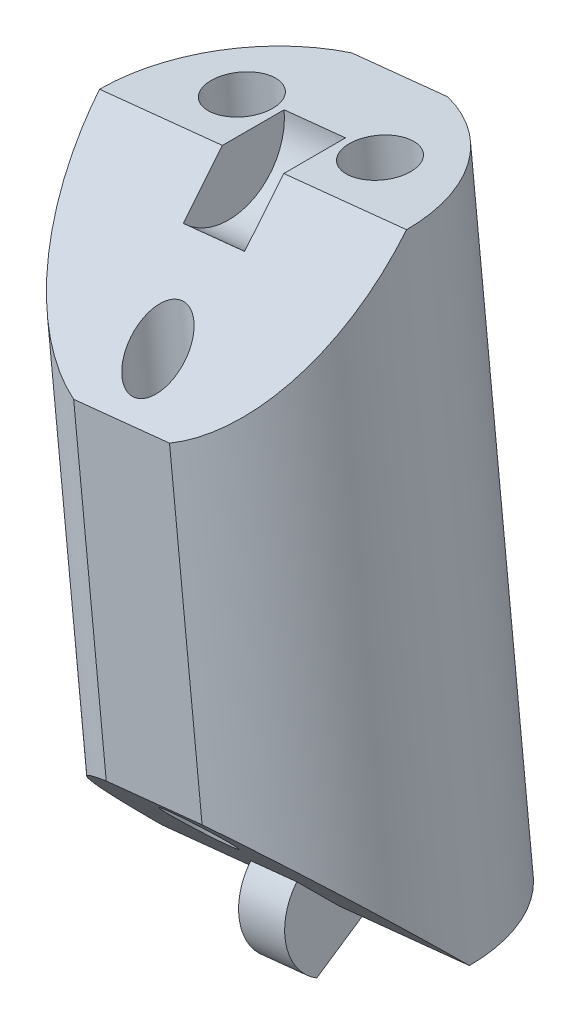
SolidWorks part; units mm, degrees
ref_plane "Front Plane" through (0, 0, 0) normal (0, 0, 1) x (1, 0, 0)
ref_plane "Top Plane" through (0, 0, 0) normal (0, 1, 0) x (1, 0, 0)
ref_plane "Right Plane" through (0, 0, 0) normal (1, 0, 0) x (0, 0, -1)
sketch "Sketch2" plane through (0, 0, 0) normal (0, 0, 1) x (1, 0, 0)
  line L0 (0, 0) -> (90, 0)
  line L1 (90, 0) -> (90, 120)
  line L2 (90, 120) -> (0, 120)
  line L3 (0, 120) -> (0, 0)
  line L4 (0, 120) -> (-10, 120)
  line L5 (-10, 120) -> (-10, 16.9491)
  line L6 (-10, 120) -> (57.5, 127)
  line L7 (57.5, 127) -> (90, 124)
  line L8 (90, 120) -> (99, 60)
  line L10 (90, 124) -> (90, 120)
  line L11 (5.9147, 0) -> (5.9147, -25)
  line L12 (5.9147, -25) -> (-4.0853, -25)
  line L13 (-4.0853, -29) -> (-4.0853, 0)
  line L14 (80, 0) -> (80, -25)
  line L15 (80, -25) -> (90, -25)
  line L16 (90, -29) -> (90, 0)
  line L17 (15.7927, 122.6748) -> (5.4776, 222.1414)
  line L18 (5.4776, 222.1414) -> (21.3923, 223.7918)
  line L19 (21.3923, 223.7918) -> (31.7073, 124.3252)
  line L20 (7.6492, 201.201) -> (23.5639, 202.8514)
  line L21 (10.9066, 169.7905) -> (26.8212, 171.441)
  line L22 (-10, 120) -> (-20.0396, 216.8108)
  line L23 (-20.0396, 216.8108) -> (-4.125, 218.4612)
  line L24 (-4.125, 218.4612) -> (5.9147, 121.6504)
  line L25 (-17.926, 196.4296) -> (-2.0114, 198.08)
  line L26 (-14.7556, 165.8578) -> (1.159, 167.5082)
  line L27 (57.5, 127) -> (46.9095, 229.1223)
  line L28 (46.9095, 229.1223) -> (30.9949, 227.4719)
  line L29 (30.9949, 227.4719) -> (41.5853, 125.3496)
  line L30 (33.2245, 205.9725) -> (49.1391, 207.6229)
  line L31 (36.5688, 173.7233) -> (52.4835, 175.3737)
  line L34 (90, 124) -> (99.1917, 223.5767)
  line L35 (99.1917, 223.5767) -> (83.2594, 225.0473)
  line L36 (83.2594, 225.0473) -> (74.0677, 125.4707)
  line L38 (81.3243, 204.0838) -> (97.2566, 202.6132)
  line L39 (78.4217, 172.6386) -> (94.354, 171.1679)
  line L40 (62.4078, 79.6749) -> (57.5, 127) construction
  line L41 (41.5853, 125.3496) -> (46.4931, 78.0244) construction
  line L42 (46.4931, 78.0244) -> (62.4078, 79.6749) construction
  line L43 (31.7073, 124.3252) -> (36.6151, 77.0001) construction
  line L44 (36.6151, 77.0001) -> (20.7005, 75.3496) construction
  line L45 (20.7005, 75.3496) -> (15.7927, 122.6748) construction
  line L46 (5.9147, 121.6504) -> (10.8224, 74.3253) construction
  line L47 (10.8224, 74.3253) -> (-5.0922, 72.6749) construction
  line L48 (-5.0922, 72.6749) -> (-10, 120) construction
  line L49 (74.0677, 125.4707) -> (69.6944, 78.0931) construction
  line L50 (69.6944, 78.0931) -> (85.7624, 78.0931) construction
  line L51 (85.7624, 78.0931) -> (90, 124) construction
  line L52 (-12.0823, 217.636) -> (10.4873, 0) construction
  line L53 (13.4349, 222.9666) -> (36.5574, 0) construction
  line L54 (38.9522, 228.2971) -> (62.6275, 0) construction
  line L55 (91.2256, 224.312) -> (70.5198, 0) construction
  line L59 (99, 60) -> (93.5277, 44.9649)
  line L60 (99, 60) -> (169.4769, 34.3485)
  line L61 (169.4769, 34.3485) -> (164.0046, 19.3134)
  line L62 (164.0046, 19.3134) -> (93.5277, 44.9649)
  line L63 (90, -2) -> (100, -2)
  line L64 (141.2862, 44.6091) -> (135.8138, 29.574)
  line L65 (99, 60) -> (55.7741, 75.7329) construction
  line L66 (55.7741, 75.7329) -> (50.3018, 60.6978) construction
  line L67 (100, -2) -> (100, -29)
  line L70 (-4.0853, -2) -> (-14.0853, -2)
  line L71 (-14.0853, -2) -> (-14.0853, -29)
  line L74 (-4.0853, 0) -> (0, 0)
  line L75 (-14.0853, -29) -> (-14.0853, -112.587)
  line L76 (-14.0853, -112.587) -> (100, -112.587)
  line L77 (100, -112.587) -> (100, -29)
  line L78 (-14.0853, -29) -> (100, -29)
  line L79 (-14.0853, -14.5) -> (100, -14.5) construction
  line L80 (31.7073, -112.587) -> (31.7073, -122.6232)
  line L81 (31.7073, -122.6232) -> (42.9573, -122.6232)
  line L82 (42.9573, -122.6232) -> (42.9573, -112.587)
  line L83 (-14.0853, -112.587) -> (-88.3667, -112.587)
  line L84 (-88.3667, -112.587) -> (-88.3667, -128.2699)
  line L85 (-88.3667, -128.2699) -> (169.4958, -128.2699)
  line L86 (169.4958, -128.2699) -> (169.4958, -112.587)
  line L87 (169.4958, -112.587) -> (100, -112.587)
  line L88 (90, 60) -> (-10, 60) construction
  line L89 (50.3018, 60.6978) -> (93.5277, 44.9649) construction
  line L90 (87.2806, 55.7521) -> (166.7408, 26.8309) construction
  line L91 (87.2806, 55.7521) -> (82.1749, 52.5336) construction
  line L92 (82.1749, 52.5336) -> (77.3257, 0) construction
  line L93 (83.1185, 56.6957) -> (86.337, 51.59) construction
  arc A0 (-10, 16.9491) -> (-4.0853, 0) centre (14.9876, 16.1624) ccw
  arc A1 (93.5277, 44.9649) -> (90, 0) centre (-126.4069, 39.5988) cw
  point P42 (41.1818, 206.7977)
  point P100 (84.7278, 54.1428)
  point P101 (84.7278, 54.1428)
  dimension "D11" = 47.3684
  dimension "D35" = 9
  dimension "D32" = 220
  dimension "D36" = 25
  dimension "D1" = 120
  dimension "D2" = 90
  dimension "D3" = 10
  dimension "D5" = 67.862
  dimension "D6" = 7
  dimension "D7" = 4
  dimension "D8" = 16
  dimension "D9" = 16
  dimension "D10" = 100
  dimension "D12" = 31.5789
  dimension "D13" = 16
  dimension "D14" = 16
  dimension "D15" = 16
  dimension "D16" = 25.7927
  dimension "D17" = 100
  dimension "D18" = 21.0526
  dimension "D19" = 31.5789
  dimension "D20" = 97.33
  dimension "D21" = 102.67
  dimension "D22" = 20.4905
  dimension "D23" = 30.7358
  dimension "D24" = 21.6147
  dimension "D25" = 32.4221
  dimension "D26" = 25
  dimension "D28" = 25
  dimension "D29" = 75
  dimension "D30" = 47.5789
  dimension "D31" = 30
  dimension "D33" = 46
  dimension "D34" = 20
  dimension "D37" = 2
  dimension "D38" = 2
  dimension "D39" = 27
  dimension "D40" = 10
  dimension "D41" = 10
  dimension "D42" = 27
  dimension "D43" = 14.5
  dimension "D44" = 127.5
ref_plane "Plane1" through (87.2806, 55.7521, 0) normal (-0.846, -0.5333, 0) x (0, 0, 1)
ref_plane "Plane2" through (82.1749, 52.5336, 0) normal (-0.0919, -0.9958, 0) x (-0.9958, 0.0919, 0)
ref_plane "Plane3" through (91.2256, 224.312, 0) normal (-0.0919, -0.9958, 0) x (-0.9958, 0.0919, 0)
ref_plane "Plane4" through (38.9522, 228.2971, 0) normal (0.1032, -0.9947, 0) x (-0.9947, -0.1032, 0)
ref_plane "Plane5" through (13.4349, 222.9666, 0) normal (0.1032, -0.9947, 0) x (-0.9947, -0.1032, 0)
ref_plane "Plane7" through (166.7408, 26.8309, 0) normal (0.9397, -0.342, 0) x (0, 0, -1)
ref_plane "Plane8" through (110.4217, -40.1902, 0) normal (0.9397, -0.342, 0) x (0, 0, -1)
ref_plane "Plane9" through (19.3664, 209.803, 0) normal (-0.0919, -0.9958, 0) x (-0.9958, 0.0919, 0)
ref_plane "Plane10" through (16.4638, 178.3578, 0) normal (-0.0919, -0.9958, 0) x (-0.9958, 0.0919, 0)
ref_plane "Plane11" through (-20.7793, 200.3721, 0) normal (0.1032, -0.9947, 0) x (-0.9947, -0.1032, 0)
ref_plane "Plane12" through (-17.435, 168.1229, 0) normal (0.1032, -0.9947, 0) x (-0.9947, -0.1032, 0)
ref_plane "Plane13" through (-20.5619, 198.2754, 0) normal (0.1032, -0.9947, 0) x (-0.9947, -0.1032, 0)
ref_plane "Plane14" through (-17.3045, 166.8649, 0) normal (0.1032, -0.9947, 0) x (-0.9947, -0.1032, 0)
ref_plane "Plane15" through (-12.0823, 217.636, 0) normal (0.1032, -0.9947, 0) x (-0.9947, -0.1032, 0)
ref_plane "Plane16" through (-20.3445, 196.1788, 0) normal (0.1032, -0.9947, 0) x (-0.9947, -0.1032, 0)
ref_plane "Plane17" through (-17.1741, 165.607, 0) normal (0.1032, -0.9947, 0) x (-0.9947, -0.1032, 0)
ref_plane "Plane18" through (12.1098, 131.1899, 0) normal (-0.0919, -0.9958, 0) x (-0.9958, 0.0919, 0)
ref_plane "Plane19" through (-12.4184, 119.7492, 0) normal (0.1032, -0.9947, 0) x (-0.9947, -0.1032, 0)
ref_plane "Plane20" through (0, 0, 0) normal (0, 0, 1) x (0.1032, -0.9947, 0)
ref_plane "Plane21" through (0, 0, 0) normal (0, 0, 1) x (-0.0919, -0.9958, 0)
ref_plane "Plane22" through (10.3758, 1.076, 0) normal (-0.9947, -0.1032, 0) x (0.1032, -0.9947, 0)
ref_plane "Plane23" through (36.1684, 3.7508, 0) normal (-0.9947, -0.1032, 0) x (0.1032, -0.9947, 0)
ref_plane "Plane24" through (61.9611, 6.4256, 0) normal (-0.9947, -0.1032, 0) x (0.1032, -0.9947, 0)
ref_plane "Plane25" through (69.924, -6.4545, 0) normal (-0.9958, 0.0919, 0) x (-0.0919, -0.9958, 0)
sketch "Sketch3" plane through (-20.3445, 196.1788, 0) normal (0.1032, -0.9947, 0) x (-0.9947, -0.1032, 0)
  line L0 (-2.4314, 0) -> (-18.4314, 0) construction
  circle A0 centre (-10.4314, 0) radius 8
  dimension "D1" = 16
extrude "Boss-Extrude1" add sketch "Sketch3" along normal blind 31.5789
sketch "Sketch4" plane through (10.3758, 1.076, 0) normal (-0.9947, -0.1032, 0) x (0.1032, -0.9947, 0)
  line L0 (-197.2309, 0) -> (-189.2309, 8)
  line L1 (-197.2309, 8) -> (-197.2309, -8) construction
  line L2 (-165.6519, 8) -> (-197.2309, 8) construction
  line L3 (-189.2309, 8) -> (-197.2309, 8)
  line L4 (-197.2309, 8) -> (-197.2309, 0)
  line L5 (-173.6519, 8) -> (-165.6519, 8)
  line L6 (-165.6519, 8) -> (-165.6519, 0)
  line L7 (-217.7214, 0) -> (1.0818, 0) construction
  line L8 (-165.6519, 0) -> (-173.6519, 8)
  dimension "D1" = 45
  dimension "D2" = 45
extrude "Cut-Extrude1" cut sketch "Sketch4" against normal through all and the other way through all
sketch "Sketch5" plane through (10.3758, 1.076, 0) normal (-0.9947, -0.1032, 0) x (0.1032, -0.9947, 0)
  line L1 (-165.6519, -2.8) -> (-163.2271, 1.4)
  line L6 (-165.6519, 0) -> (-173.6519, 8) construction
  line L11 (-165.6519, -8) -> (-165.6519, 0) construction
  line L12 (-167.6318, 1.9799) -> (-165.6519, 0)
  line L13 (-165.6519, 0) -> (-165.6519, -2.8)
  arc A3 (-167.6318, 1.9799) -> (-163.2271, 1.4) centre (-165.6519, 0) cw
  dimension "D2" = 2.8
  dimension "D1" = 30
  dimension "D3" = 2.8
extrude "Boss-Extrude2" add sketch "Sketch5" along normal mid plane 2.4
sketch "Sketch7" plane through (10.3758, 1.076, 0) normal (-0.9947, -0.1032, 0) x (0.1032, -0.9947, 0)
  line L6 (-197.2309, 0) -> (-197.2309, -8) construction
  line L7 (-189.2309, 8) -> (-197.2309, 0) construction
  line L8 (-194.9681, 2.2627) -> (-197.2309, 0)
  line L9 (-197.2309, 0) -> (-197.2309, -3.2)
  arc A1 (-197.2309, -3.2) -> (-194.9681, 2.2627) centre (-197.2309, 0) ccw
  dimension "D1" = 3.2
extrude "Cut-Extrude2" cut sketch "Sketch7" against normal mid plane 3.2
sketch "Sketch8" plane through (-20.3445, 196.1788, 0) normal (-0.1032, 0.9947, 0) x (0.9947, 0.1032, 0)
  line L0 (2.4314, 0) -> (18.4314, 0) construction
  circle A0 centre (10.4314, -5.5) radius 1.4
  circle A1 centre (6.8314, 3) radius 1.6
  circle A2 centre (14.0314, 3) radius 1.6
  point P9 (10.4314, 0)
  dimension "D1" = 3.2
  dimension "D2" = 3.2
  dimension "D3" = 2.8
  dimension "D4" = 3
  dimension "D5" = 5.5
  dimension "D6" = 3.6
  dimension "D7" = 3.6
  dimension "D8" = 3
extrude "Cut-Extrude3" cut sketch "Sketch8" against normal through all and the other way through all
sketch "Sketch9" plane through (-20.3445, 196.1788, 0) normal (-0.1032, 0.9947, 0) x (0.9947, 0.1032, 0)
  line L0 (7.9334, 7.6) -> (12.9294, 7.6)
  line L1 (-101.1265, 0) -> (155.3606, 0) construction
  line L2 (7.9334, -7.6) -> (12.9294, -7.6)
  arc A0 (18.4314, 0) -> (2.4314, 0) centre (10.4314, 0) ccw construction
  arc A1 (7.9334, 7.6) -> (12.9294, 7.6) centre (10.4314, 0) cw
  arc A2 (2.4314, 0) -> (18.4314, 0) centre (10.4314, 0) ccw construction
  arc A3 (7.9334, -7.6) -> (12.9294, -7.6) centre (10.4314, 0) ccw
  dimension "D1" = 7.6
  dimension "D2" = 7.6
extrude "Cut-Extrude4" cut sketch "Sketch9" against normal through all
